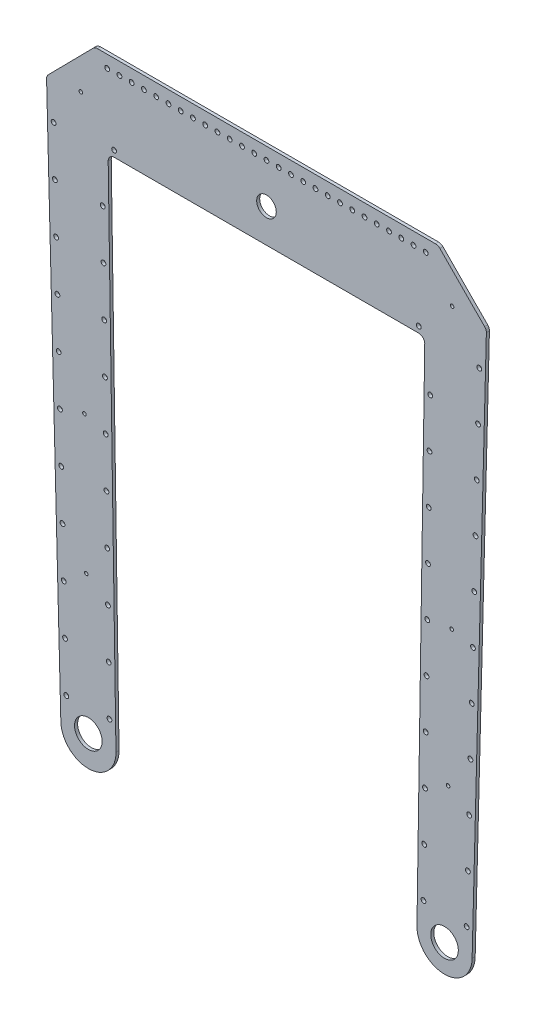
SolidWorks part; units mm, degrees
material "PPE"
ref_plane "Front Plane" through (0, 0, 0) normal (0, 0, 1) x (1, 0, 0)
ref_plane "Top Plane" through (0, 0, 0) normal (0, 1, 0) x (1, 0, 0)
ref_plane "Right Plane" through (0, 0, 0) normal (1, 0, 0) x (0, 0, -1)
sketch "Sketch1" plane through (0, 0, 0) normal (0, 0, 1) x (1, 0, 0)
  line L0 (25.4, 25.4) -> (25.4, 0)
  line L1 (0, 0) -> (508, 0) construction
  line L2 (0, 0) -> (0, 25.4) construction
  line L3 (0, 25.4) -> (508, 25.4) construction
  line L4 (508, 0) -> (508, 25.4) construction
  line L5 (482.6, 25.4) -> (482.6, 0)
  line L6 (25.4, 25.4) -> (482.6, 25.4)
  line L7 (25.4, 0) -> (40.894, -596.9)
  line L8 (254, 25.4) -> (254, 0) construction
  line L9 (482.6, 0) -> (467.106, -596.9)
  line L10 (88.9, 0) -> (98.0406, -596.4621)
  line L11 (419.1, 0) -> (409.9594, -596.4621)
  line L12 (88.9, 0) -> (419.1, 0)
  line L13 (89.8731, -63.5) -> (418.1269, -63.5)
  line L19 (33.4004, -63.5) -> (34.7186, -114.2829) construction
  line L20 (34.7186, -114.2829) -> (84.2809, -112.9964) construction
  line L21 (84.2809, -112.9964) -> (85.0593, -163.7904) construction
  line L22 (473.2814, -114.2829) -> (423.7191, -112.9964) construction
  line L23 (423.7191, -112.9964) -> (422.9407, -163.7904) construction
  line L24 (76.2, 25.4) -> (26.0593, -25.4)
  line L25 (431.8, 25.4) -> (481.9407, -25.4)
  line L26 (88.9, 12.7) -> (101.6, 12.7) construction
  circle A0 centre (69.469, -596.9) radius 50.8 construction
  circle A1 centre (438.531, -596.9) radius 50.8 construction
  arc A2 (40.894, -596.9) -> (98.0406, -596.4621) centre (69.469, -596.9) ccw
  circle A3 centre (69.469, -596.9) radius 14.2875 construction
  circle A4 centre (438.531, -596.9) radius 14.2875
  arc A5 (467.106, -596.9) -> (409.9594, -596.4621) centre (438.531, -596.9) cw
  circle A6 centre (254, -28.575) radius 10.16
  circle A7 centre (254, -28.575) radius 25.4 construction
  circle A22 centre (254, -28.575) radius 192.5 construction
  circle A24 centre (438.531, -596.9) radius 142.5 construction
  circle A25 centre (442.2191, -454.4477) radius 142.5 construction
  circle A28 centre (442.2191, -454.4477) radius 1.8288
  circle A29 centre (61.6125, -21.9961) radius 1.8288
  circle A32 centre (33.4004, -63.5) radius 2.4892
  circle A33 centre (33.4004, -63.5) radius 6.35 construction
  circle A34 centre (34.7186, -114.2829) radius 2.4892
  circle A35 centre (36.0368, -165.0658) radius 2.4892
  circle A36 centre (37.355, -215.8487) radius 2.4892
  circle A37 centre (38.6732, -266.6316) radius 2.4892
  circle A38 centre (39.9914, -317.4145) radius 2.4892
  circle A39 centre (41.3096, -368.1974) radius 2.4892
  circle A40 centre (42.6278, -418.9803) radius 2.4892
  circle A41 centre (43.946, -469.7632) radius 2.4892
  circle A42 centre (45.2642, -520.546) radius 2.4892
  circle A43 centre (46.5824, -571.3289) radius 2.4892
  circle A44 centre (474.5996, -63.5) radius 2.4892
  circle A45 centre (461.4176, -571.3289) radius 2.4892
  circle A46 centre (462.7358, -520.546) radius 2.4892
  circle A47 centre (464.054, -469.7632) radius 2.4892
  circle A48 centre (465.3722, -418.9803) radius 2.4892
  circle A49 centre (466.6904, -368.1974) radius 2.4892
  circle A50 centre (468.0086, -317.4145) radius 2.4892
  circle A51 centre (469.3268, -266.6316) radius 2.4892
  circle A52 centre (470.645, -215.8487) radius 2.4892
  circle A53 centre (471.9632, -165.0658) radius 2.4892
  circle A54 centre (473.2814, -114.2829) radius 2.4892
  circle A55 centre (96.1266, -57.15) radius 2.4892
  circle A57 centre (411.8734, -57.15) radius 2.4892
  circle A58 centre (84.2809, -112.9964) radius 2.4892
  circle A59 centre (85.0593, -163.7904) radius 2.4892
  circle A60 centre (85.8377, -214.5845) radius 2.4892
  circle A61 centre (86.6161, -265.3785) radius 2.4892
  circle A62 centre (87.3945, -316.1725) radius 2.4892
  circle A63 centre (88.1729, -366.9666) radius 2.4892
  circle A64 centre (88.9513, -417.7606) radius 2.4892
  circle A65 centre (89.7297, -468.5546) radius 2.4892
  circle A66 centre (90.5082, -519.3487) radius 2.4892
  circle A67 centre (91.2866, -570.1427) radius 2.4892
  circle A68 centre (423.7191, -112.9964) radius 2.4892
  circle A69 centre (422.9407, -163.7904) radius 2.4892
  circle A70 centre (422.1623, -214.5845) radius 2.4892
  circle A71 centre (421.3839, -265.3785) radius 2.4892
  circle A72 centre (420.6055, -316.1725) radius 2.4892
  circle A73 centre (419.8271, -366.9666) radius 2.4892
  circle A74 centre (419.0487, -417.7606) radius 2.4892
  circle A75 centre (418.2703, -468.5546) radius 2.4892
  circle A76 centre (417.4918, -519.3487) radius 2.4892
  circle A77 centre (416.7134, -570.1427) radius 2.4892
  circle A82 centre (61.6125, -21.9961) radius 287.02 construction
  circle A84 centre (67.2405, -451.4792) radius 142.5 construction
  circle A86 centre (69.4024, -593.9628) radius 14.2875
  circle A87 centre (67.2405, -451.4792) radius 1.8288
  circle A88 centre (65.3733, -308.9915) radius 1.8288
  circle A89 centre (446.3875, -21.9961) radius 1.8288
  circle A90 centre (446.3875, -21.9961) radius 290 construction
  circle A91 centre (445.9168, -311.9957) radius 1.8288
  circle A92 centre (88.9, 12.7) radius 2.4892
  circle A93 centre (101.6, 12.7) radius 2.4892
  circle A94 centre (114.3, 12.7) radius 2.4892
  circle A95 centre (127, 12.7) radius 2.4892
  circle A96 centre (139.7, 12.7) radius 2.4892
  circle A97 centre (152.4, 12.7) radius 2.4892
  circle A98 centre (165.1, 12.7) radius 2.4892
  circle A99 centre (177.8, 12.7) radius 2.4892
  circle A100 centre (190.5, 12.7) radius 2.4892
  circle A101 centre (203.2, 12.7) radius 2.4892
  circle A102 centre (215.9, 12.7) radius 2.4892
  circle A103 centre (228.6, 12.7) radius 2.4892
  circle A104 centre (241.3, 12.7) radius 2.4892
  circle A105 centre (254, 12.7) radius 2.4892
  circle A106 centre (266.7, 12.7) radius 2.4892
  circle A107 centre (279.4, 12.7) radius 2.4892
  circle A108 centre (292.1, 12.7) radius 2.4892
  circle A109 centre (304.8, 12.7) radius 2.4892
  circle A110 centre (317.5, 12.7) radius 2.4892
  circle A111 centre (330.2, 12.7) radius 2.4892
  circle A112 centre (342.9, 12.7) radius 2.4892
  circle A113 centre (355.6, 12.7) radius 2.4892
  circle A114 centre (368.3, 12.7) radius 2.4892
  circle A115 centre (381, 12.7) radius 2.4892
  circle A116 centre (393.7, 12.7) radius 2.4892
  circle A117 centre (406.4, 12.7) radius 2.4892
  circle A118 centre (419.1, 12.7) radius 2.4892
  dimension "D4" = 101.6
  dimension "D6" = 267.462
  dimension "D7" = 28.575
  dimension "D8" = 28.575
  dimension "D11" = 20.32
  dimension "D13" = 50.8
  dimension "D20" = 385
  dimension "D21" = 285
  dimension "D22" = 580
  dimension "D24" = 28.575
  dimension "D25" = 4.9784
  dimension "D26" = 12.7
  dimension "D39" = 574.04
  dimension "D40" = 28.575
  dimension "D42" = 3.6576
  dimension "D43" = 12.7
  dimension "D44" = 4.9784
  dimension "D1" = 508
  dimension "D2" = 25.4
  dimension "D3" = 25.4
  dimension "D5" = 596.9
  dimension "D9" = 63.5
  dimension "D10" = 63.5
  dimension "D12" = 28.575
  dimension "D23" = 28.575
  dimension "D27" = 11
  dimension "D28" = 50.8
  dimension "D29" = 6.35
  dimension "D30" = 6.35
  dimension "D31" = 6.35
  dimension "D33" = 50.8
  dimension "D34" = 6.35
  dimension "D36" = 50.8
  dimension "D37" = 50.8
  dimension "D38" = 50.8
  dimension "D41" = 28.575
  dimension "D46" = 12.7
  dimension "D32" = 10
  dimension "D35" = 10
  dimension "D45" = 27
extrude "Boss-Extrude1" add sketch "Sketch1" along normal blind 3.175
fillet "Fillet1" radius 6.35 6 edges at (418.1269, -63.5, 1.5875) (89.8731, -63.5, 1.5875) (481.9407, -25.4, 1.5875) (431.8, 25.4, 1.5875) (76.2, 25.4, 1.5875) (26.0593, -25.4, 1.5875)
sketch "Sketch2" plane through (0, 0, 3.175) normal (0, 0, 1) x (1, 0, 0)
  line L0 (456.8703, 0) -> (476.0123, -253.7903)
  line L1 (433.6648, 23.5107) -> (480.042, -23.4764) construction
  line L2 (481.8705, -28.1019) -> (467.106, -596.9) construction
  line L3 (78.8546, 25.4) -> (429.1454, 25.4) construction
  dimension "D1" = 25.4
